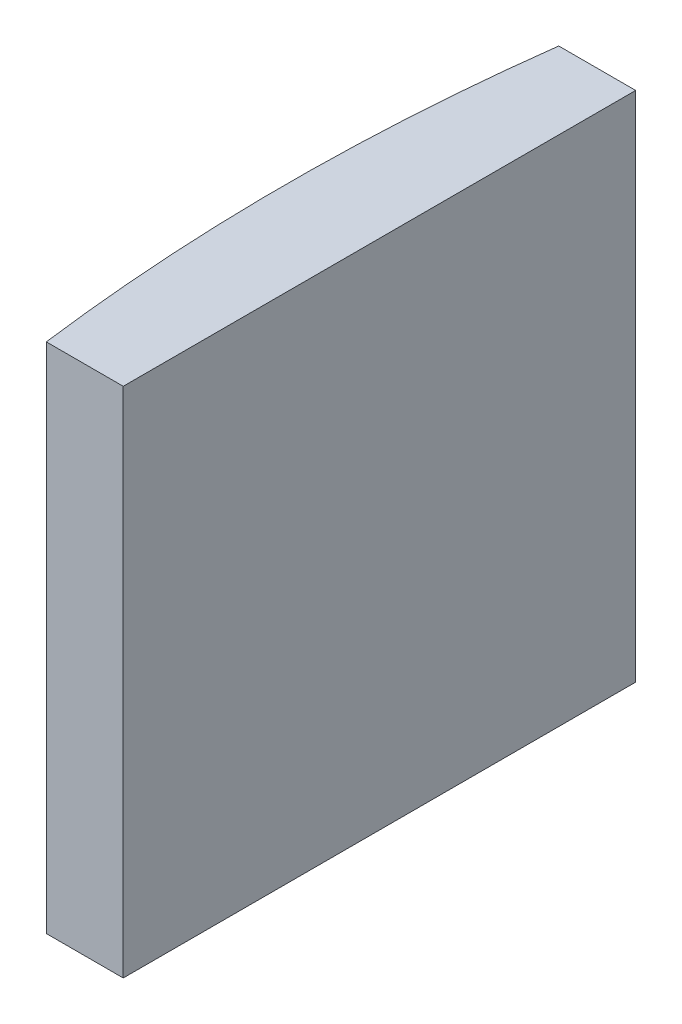
SolidWorks part; units mm, degrees
ref_plane "前视基准面" through (0, 0, 0) normal (0, 0, 1) x (1, 0, 0)
ref_plane "上视基准面" through (0, 0, 0) normal (0, 1, 0) x (1, 0, 0)
ref_plane "右视基准面" through (0, 0, 0) normal (1, 0, 0) x (0, 0, -1)
sketch "草图1" plane through (0, 0, 0) normal (0, 1, 0) x (1, 0, 0)
  line L0 (10.7432, 0) -> (-85.4992, 0) construction
  line L1 (-72.5473, 10) -> (-69.5448, 10)
  line L2 (-72.5473, -10) -> (-69.5448, -10)
  line L3 (-69.5448, 10) -> (-69.5448, -10)
  arc A0 (-72.5473, 10) -> (-72.5473, -10) centre (4.3552, 0) ccw
  point P2 (-85.4992, 0)
  point P19 (-73.1948, 0)
  point P20 (-69.5448, 0)
  dimension "D2" = 10
  dimension "D3" = 77.55
  dimension "D4" = 3.65
  dimension "D1" = 10
extrude "凸台-拉伸1" add sketch "草图1" along normal blind 20
